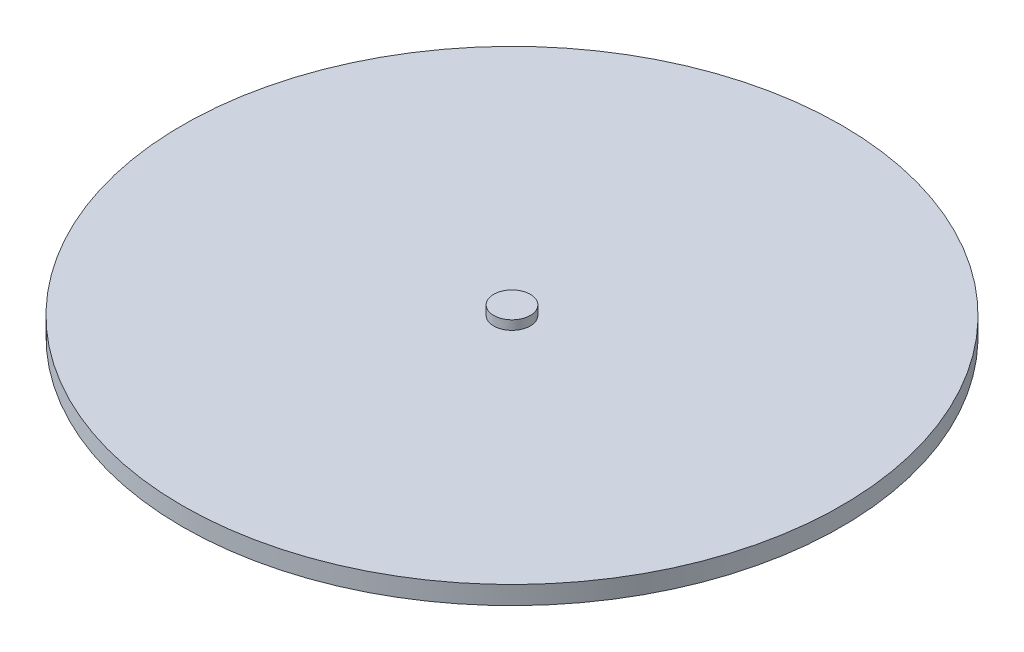
SolidWorks part; units mm, degrees
material "AISI 304"
ref_plane "Front Plane" through (0, 0, 0) normal (0, 0, 1) x (1, 0, 0)
ref_plane "Top Plane" through (0, 0, 0) normal (0, 1, 0) x (1, 0, 0)
ref_plane "Right Plane" through (0, 0, 0) normal (1, 0, 0) x (0, 0, -1)
sketch "Sketch1" plane through (0, 0, 0) normal (0, 1, 0) x (1, 0, 0)
  circle A0 centre (0, 0) radius 228.6
extrude "Boss-Extrude1" add sketch "Sketch1" along normal mid plane 12.7
sketch "Sketch2" plane through (0, 6.35, 0) normal (0, 1, 0) x (1, 0, 0)
  circle A0 centre (0, 0) radius 12.7
extrude "Boss-Extrude2" add sketch "Sketch2" along normal blind 6.35
